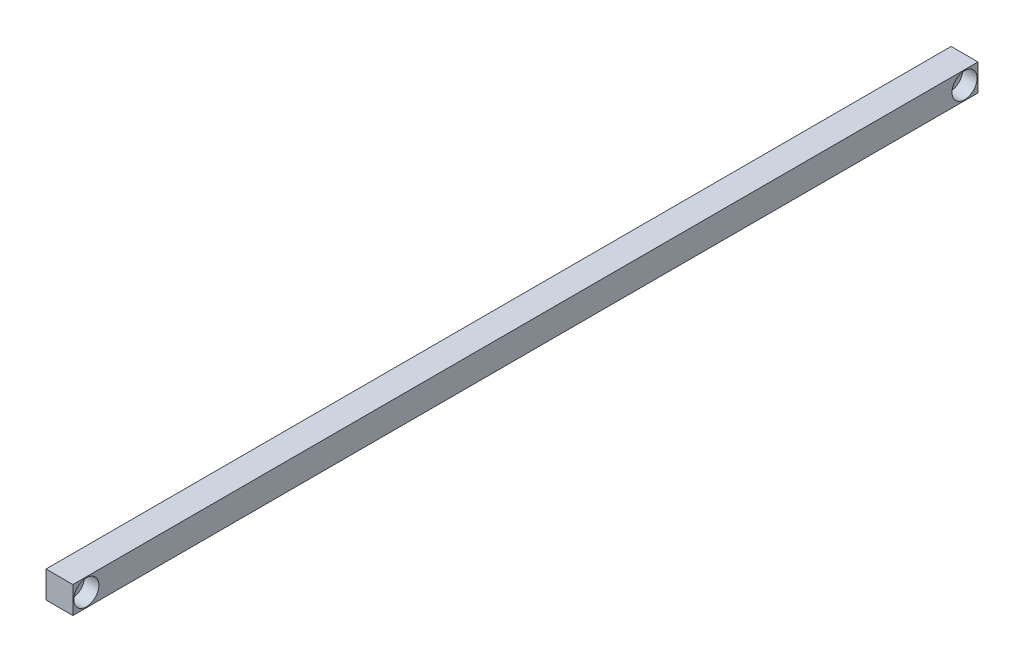
SolidWorks part; units mm, degrees
ref_plane "Front Plane" through (0, 0, 0) normal (0, 0, 1) x (1, 0, 0)
ref_plane "Top Plane" through (0, 0, 0) normal (0, 1, 0) x (1, 0, 0)
ref_plane "Right Plane" through (0, 0, 0) normal (1, 0, 0) x (0, 0, -1)
sketch "Çizim1" plane through (0, 0, 0) normal (0, 0, 1) x (1, 0, 0)
  line L1 (-7.5, 7.5) -> (7.5, 7.5)
  line L2 (-7.5, 7.5) -> (-7.5, -7.5)
  line L3 (-7.5, -7.5) -> (7.5, -7.5)
  line L4 (7.5, 7.5) -> (7.5, -7.5)
  line L5 (-7.5, 7.5) -> (7.5, -7.5) construction
  line L6 (-7.5, -7.5) -> (7.5, 7.5) construction
  point P0 (0, 0)
  dimension "D1" = 15
extrude "Yükseklik-Ekstrüzyon1" add sketch "Çizim1" along normal mid plane 505
hole_wizard "Delik2" positions "Çizim5" profile "Çizim6" legacy
sketch "Çizim5" plane through (7.5, 0, 0) normal (1, 0, 0) x (0, 0, -1)
  line L0 (252.5, -7.5) -> (252.5, 7.5) construction
  line L1 (-252.5, 7.5) -> (252.5, 7.5) construction
  point P0 (245, 0)
  dimension "D1" = 7.5
  dimension "D2" = 7.5
sketch "Çizim6" plane through (7.5, 0, -245) normal (0, 1, 0) x (0, 0, -1)
  line L0 (0, 0) -> (0, 15)
  line L1 (0, 15) -> (4.25, 15)
  line L2 (4.25, 15) -> (4.25, 8)
  line L3 (4.25, 8) -> (7, 8)
  line L4 (7, 8) -> (7, 0)
  line L5 (7, 0) -> (0, 0)
  line L6 (0, 110) -> (0, -10) construction
  dimension "Diameter" = 8.5
  dimension "Depth" = 15
  dimension "C-Bore Diameter" = 14
  dimension "C-Bore Depth" = 8
mirror "Aynalama1" about plane through (0, 0, 0) normal (0, 0, 1) of "Delik2"
